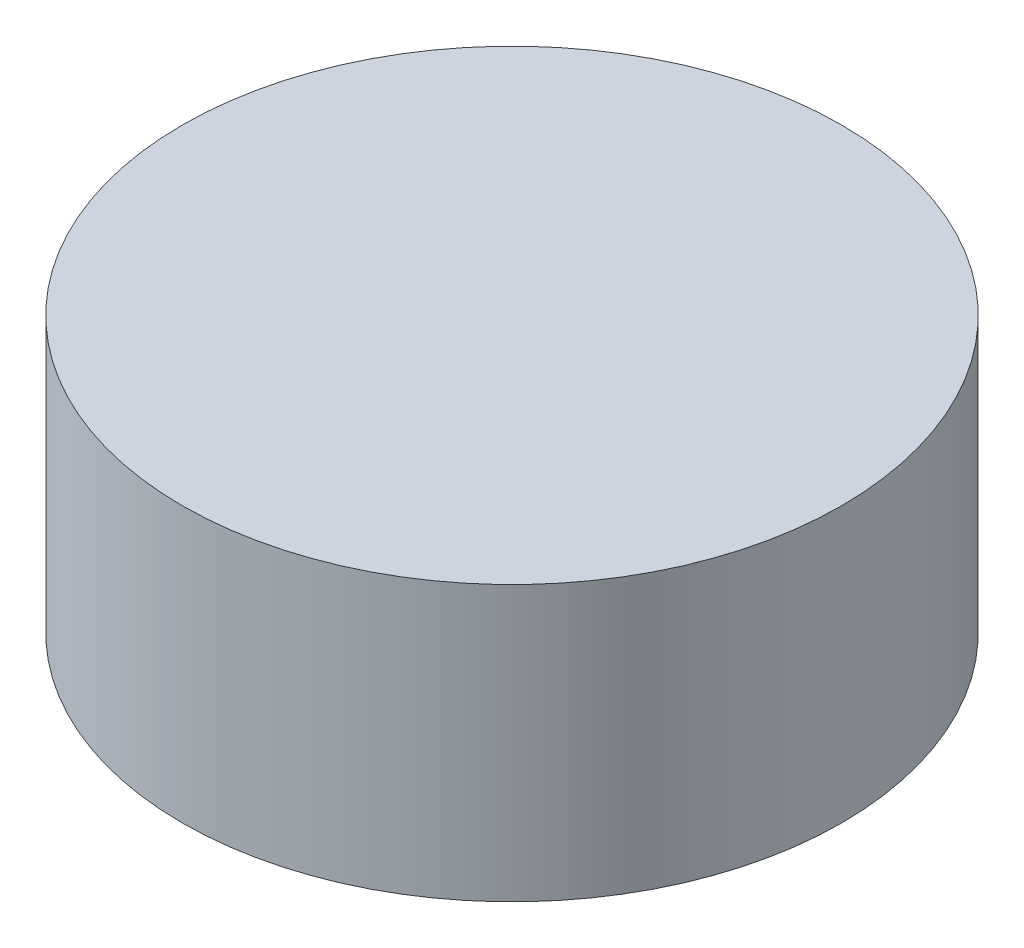
SolidWorks part; units mm, degrees
ref_plane "Front Plane" through (0, 0, 0) normal (0, 0, 1) x (1, 0, 0)
ref_plane "Top Plane" through (0, 0, 0) normal (0, 1, 0) x (1, 0, 0)
ref_plane "Right Plane" through (0, 0, 0) normal (1, 0, 0) x (0, 0, -1)
sketch "Sketch1" plane through (0, 0, 0) normal (0, 1, 0) x (1, 0, 0)
  circle A0 centre (0, 0) radius 3
  dimension "D1" = 6
extrude "Boss-Extrude1" add sketch "Sketch1" along normal blind 2.5
